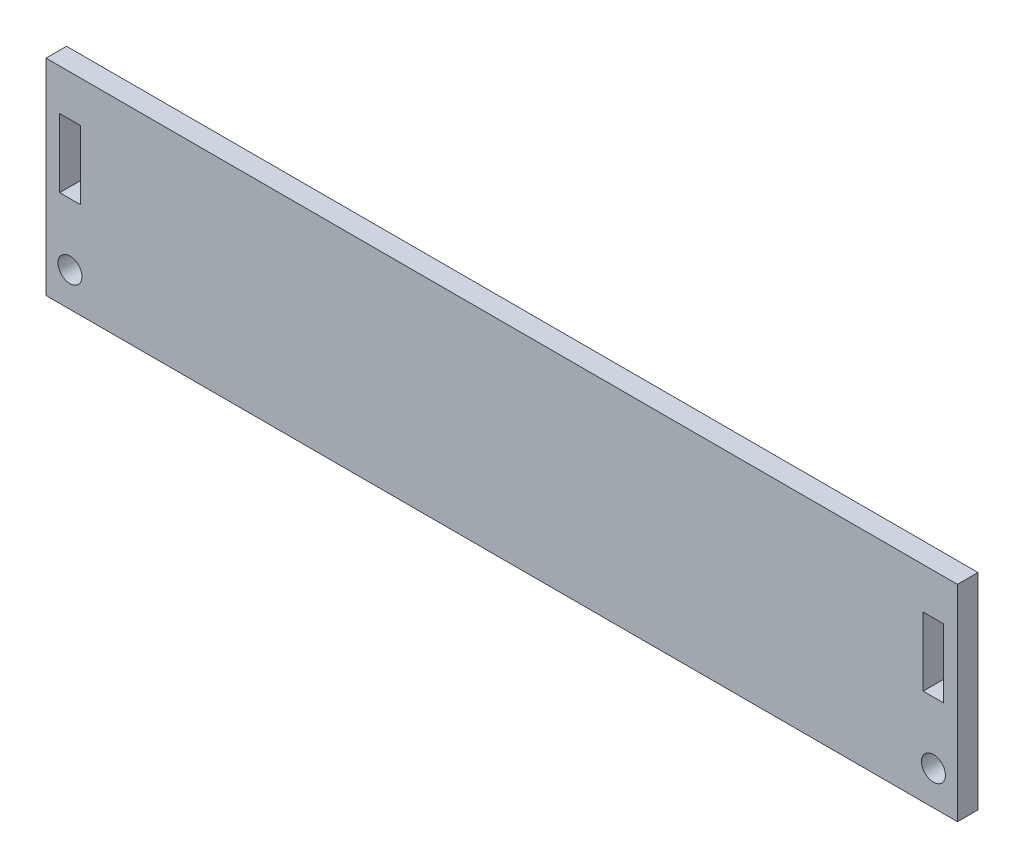
SolidWorks part; units mm, degrees
ref_plane "Front Plane" through (0, 0, 0) normal (0, 0, 1) x (1, 0, 0)
ref_plane "Top Plane" through (0, 0, 0) normal (0, 1, 0) x (1, 0, 0)
ref_plane "Right Plane" through (0, 0, 0) normal (1, 0, 0) x (0, 0, -1)
sketch "Sketch1" plane through (0, 0, 0) normal (0, 0, 1) x (1, 0, 0)
  line L0 (64.5, 11.5) -> (64.5, 1.5)
  line L1 (-66.5, 17.5) -> (66.5, 17.5)
  line L2 (-66.5, 17.5) -> (-66.5, -12.5)
  line L4 (66.5, 17.5) -> (66.5, -12.5)
  line L7 (-64.5, 11.5) -> (-61.5, 11.5)
  line L8 (-64.5, 11.5) -> (-64.5, 1.5)
  line L9 (-64.5, 1.5) -> (-61.5, 1.5)
  line L10 (-61.5, 11.5) -> (-61.5, 1.5)
  line L11 (-64.5, 11.5) -> (-61.5, 1.5) construction
  line L12 (-64.5, 1.5) -> (-61.5, 11.5) construction
  line L13 (61.5, 11.5) -> (61.5, 1.5)
  line L14 (61.5, 1.5) -> (64.5, 1.5)
  line L15 (61.5, 1.5) -> (64.5, 11.5) construction
  line L16 (61.5, 11.5) -> (64.5, 11.5)
  line L17 (61.5, 11.5) -> (64.5, 1.5) construction
  line L19 (-66.5, -12.5) -> (66.5, -12.5)
  circle A0 centre (-63, -7.5) radius 1.75
  circle A1 centre (63, -7.5) radius 1.75
  point P0 (0, 0)
  point P6 (-63, 6.5)
  point P11 (0, -15)
  point P12 (63, 6.5)
  dimension "D1" = 133
  dimension "D2" = 30
extrude "Boss-Extrude1" add sketch "Sketch1" along normal blind 3
